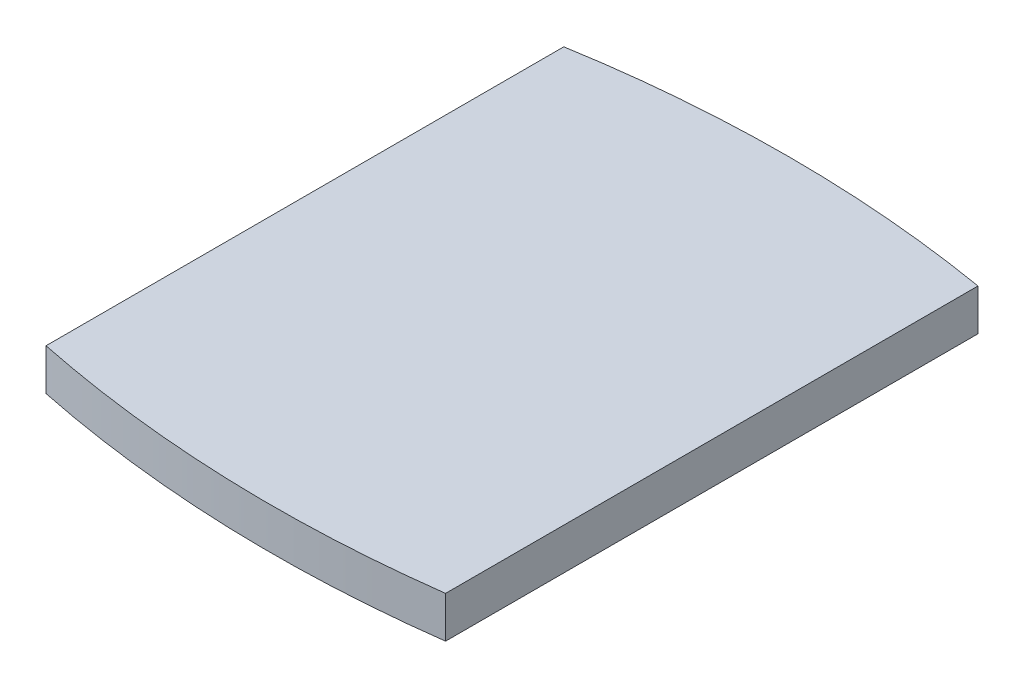
SolidWorks part; units mm, degrees
ref_plane "Спереди" through (0, 0, 0) normal (0, 0, 1) x (1, 0, 0)
ref_plane "Сверху" through (0, 0, 0) normal (0, 1, 0) x (1, 0, 0)
ref_plane "Справа" through (0, 0, 0) normal (1, 0, 0) x (0, 0, -1)
sketch "Эскиз1" plane through (0, 0, 0) normal (0, 1, 0) x (1, 0, 0)
  line L0 (0, 0) -> (0, 25)
  line L1 (20, 25) -> (20, -0.707)
  arc A0 (0, 25) -> (20, 25) centre (10, -34.1608) cw
  arc A1 (0, 0) -> (20, -0.707) centre (12.09, 58.7693) ccw
extrude "Бобышка-Вытянуть1" add sketch "Эскиз1" along normal blind 2
